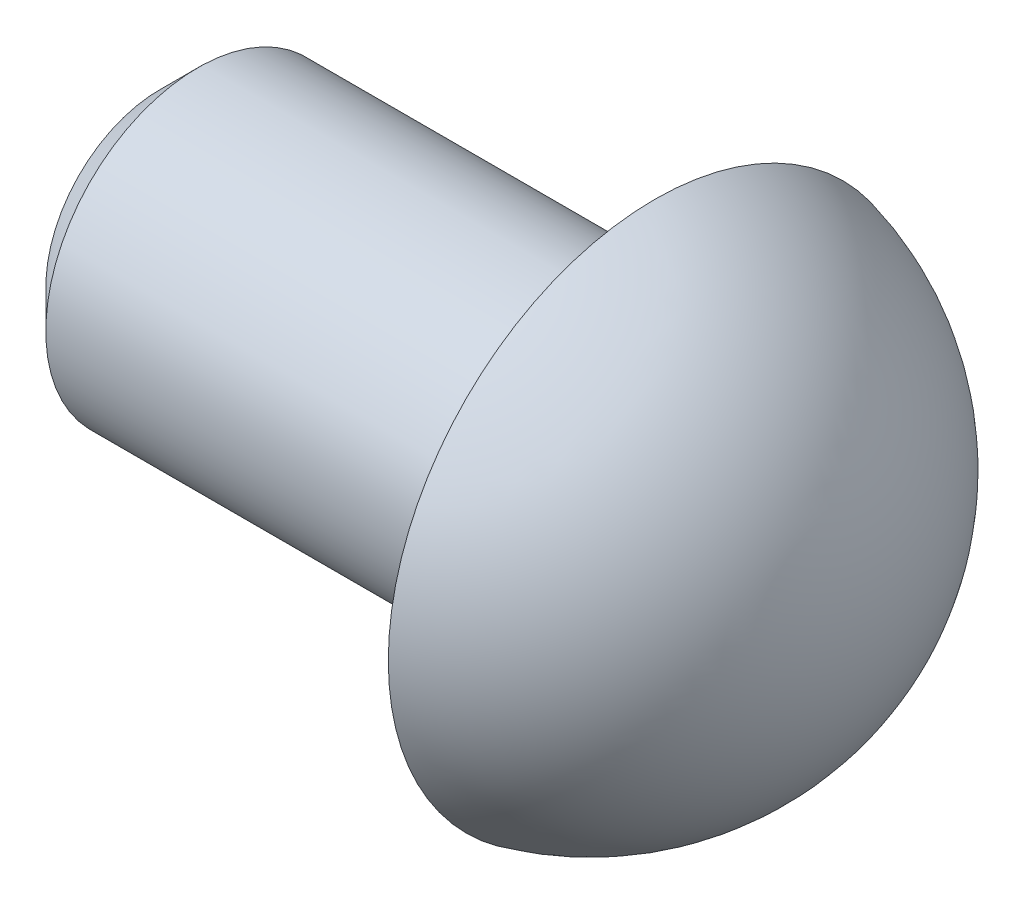
SolidWorks part; units mm, degrees
ref_plane "Front Plane" through (0, 0, 0) normal (0, 0, 1) x (1, 0, 0)
ref_plane "Top Plane" through (0, 0, 0) normal (0, 1, 0) x (1, 0, 0)
ref_plane "Right Plane" through (0, 0, 0) normal (1, 0, 0) x (0, 0, -1)
sketch "Sketch1" plane through (0, 0, 0) normal (1, 0, 0) x (0, 0, -1)
  circle A0 centre (0, 0) radius 2
  dimension "D1" = 4
extrude "Boss-Extrude1" add sketch "Sketch1" against normal blind 6.5
sketch "Sketch2" plane through (0, 0, 0) normal (0, 1, 0) x (1, 0, 0)
  line L0 (-2.547, 0) -> (3.0281, 0) construction
  line L1 (2.7574, 0) -> (0, 0)
  line L2 (0, 0) -> (0, 3.5)
  arc A0 (0, 3.5) -> (2.7574, 0) centre (-0.8426, 0) cw
  dimension "D2" = 3.6
  dimension "D1" = 3.5
revolve "Revolve1" add sketch "Sketch2" angle 360 about L0
chamfer "Chamfer1" distance 0.5 angle 45 1 edges at (-6.5, 0, -2)
